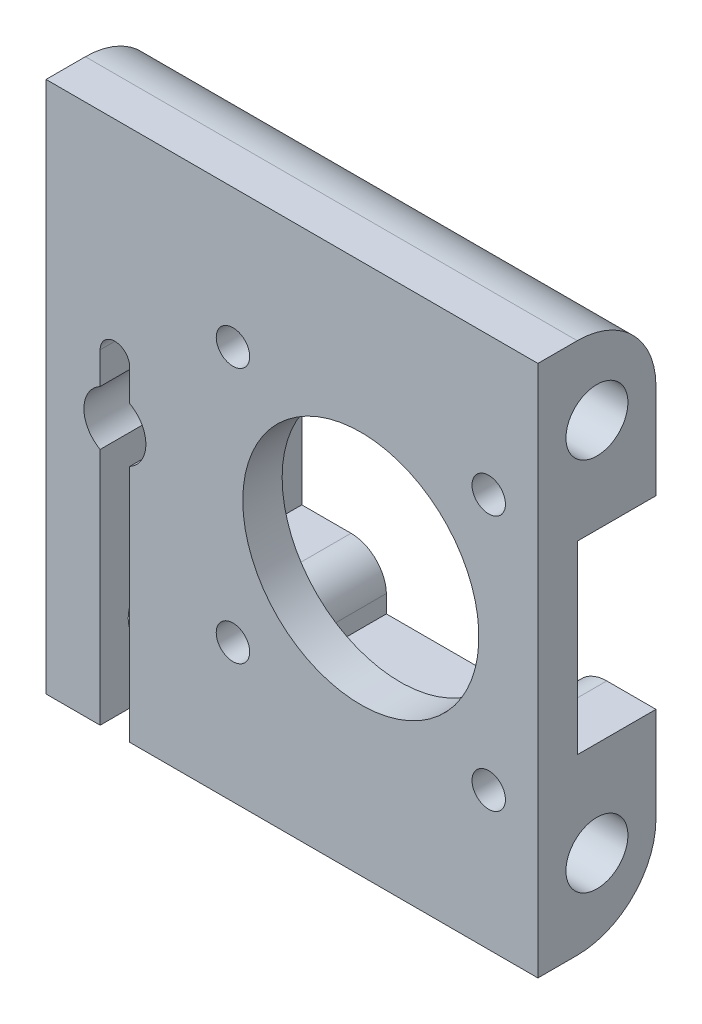
SolidWorks part; units mm, degrees
ref_plane "Front Plane" through (0, 0, 0) normal (0, 0, 1) x (1, 0, 0)
ref_plane "Top Plane" through (0, 0, 0) normal (0, 1, 0) x (1, 0, 0)
ref_plane "Right Plane" through (0, 0, 0) normal (1, 0, 0) x (0, 0, -1)
sketch "Sketch1" plane through (0, 0, 0) normal (0, 0, 1) x (1, 0, 0)
  line L1 (0, 0) -> (50, 0)
  line L2 (0, 0) -> (0, 54.105)
  line L3 (0, 54.105) -> (50, 54.105)
  line L4 (50, 0) -> (50, 54.105)
  dimension "D1" = 54.105
  dimension "D2" = 50
extrude "Boss-Extrude1" add sketch "Sketch1" along normal blind 12
sketch "Sketch2" plane through (0, 0, 0) normal (1, 0, 0) x (0, 0, -1)
  line L0 (-12, 27.0525) -> (0, 27.0525) construction
  line L1 (-12, 0) -> (-12, 54.105) construction
  line L2 (0, 0) -> (0, 54.105) construction
  circle A0 centre (-6, 46.105) radius 3.15
  circle A1 centre (-6, 8) radius 3.15
  dimension "D2" = 6.3
  dimension "D1" = 6
  dimension "D3" = 19.0525
extrude "Cut-Extrude1" cut sketch "Sketch2" along normal through all
fillet "Fillet1" radius 8 2 edges at (25, 0, 0) (25, 54.105, 0)
sketch "Sketch3" plane through (0, 0, 0) normal (0, 0, -1) x (-1, 0, 0)
  line L0 (-50, 27.0525) -> (0, 27.0525) construction
  line L1 (-50, 8) -> (-50, 46.105) construction
  line L2 (0, 46.105) -> (0, 8) construction
  line L3 (-8.5, 0) -> (-8.5, 24.2826)
  line L5 (-5.5, 33.0525) -> (-5.5, 29.8224)
  line L6 (0, 0) -> (-50, 0) construction
  line L7 (-8.5, 0) -> (-5.5, 0)
  line L8 (-8.5, 29.8224) -> (-8.5, 33.0525)
  line L9 (-5.5, 24.2826) -> (-5.5, 0)
  arc A0 (-8.5, 29.8224) -> (-8.5, 24.2826) centre (-7, 27.0525) ccw
  circle A1 centre (-32, 27.0525) radius 12
  circle A2 centre (-19, 40.0525) radius 1.7
  circle A3 centre (-19, 14.0525) radius 1.7
  arc A4 (-5.5, 24.2826) -> (-5.5, 29.8224) centre (-7, 27.0525) ccw
  arc A5 (-5.5, 33.0525) -> (-8.5, 33.0525) centre (-7, 33.0525) ccw
  circle A6 centre (-45, 14.0525) radius 1.7
  circle A7 centre (-45, 40.0525) radius 1.7
  dimension "D1" = 24
  dimension "D2" = 6.3
  dimension "D5" = 3.4
  dimension "D6" = 1.5
  dimension "D7" = 13
  dimension "D10" = 13
  dimension "D3" = 7
  dimension "D4" = 25
  dimension "D8" = 3
  dimension "D9" = 6
  dimension "D11" = 4
extrude "Cut-Extrude2" cut sketch "Sketch3" against normal through all
sketch "Sketch5" plane through (0, 0, 0) normal (0, 0, -1) x (-1, 0, 0)
  line L0 (-50, 27.0525) -> (-29.1332, 27.0525) construction
  line L1 (-19, 17.6525) -> (-14, 17.6525)
  line L2 (-50, 36.4525) -> (-50, 17.6525)
  line L4 (-14, 36.4525) -> (-14, 17.6525)
  line L5 (-50, 8) -> (-50, 46.105) construction
  line L7 (0, 46.105) -> (0, 8) construction
  line L8 (-41.4013, 41.7525) -> (-22.5987, 41.7525)
  line L9 (-22.5987, 41.7525) -> (-22.5987, 39.955)
  line L10 (-41.4013, 39.955) -> (-41.4013, 41.7525)
  line L11 (-45, 36.4525) -> (-50, 36.4525)
  line L12 (-19, 36.4525) -> (-14, 36.4525)
  line L13 (-45, 17.6525) -> (-50, 17.6525)
  line L14 (-41.4013, 14.15) -> (-41.4013, 12.3525)
  line L15 (-22.5987, 12.3525) -> (-22.5987, 14.15)
  line L16 (-41.4013, 12.3525) -> (-22.5987, 12.3525)
  arc A0 (-45, 36.4525) -> (-41.4013, 39.955) centre (-45, 40.0525) ccw
  arc A1 (-22.5987, 39.955) -> (-19, 36.4525) centre (-19, 40.0525) ccw
  circle A2 centre (-45, 40.0525) radius 1.7 construction
  circle A3 centre (-19, 40.0525) radius 1.7 construction
  arc A4 (-22.5987, 14.15) -> (-19, 17.6525) centre (-19, 14.0525) cw
  arc A5 (-45, 17.6525) -> (-41.4013, 14.15) centre (-45, 14.0525) cw
  dimension "D5" = 3.6
  dimension "D4" = 14
extrude "Cut-Extrude4" cut sketch "Sketch5" against normal offset from surface (8 mm away) 4 up to face at (43.3, 40.0525, 12)
sketch "Sketch4" plane through (0, 0, 0) normal (0, 0, -1) x (-1, 0, 0)
  circle A0 centre (-32, 27.0525) radius 6.7
  circle A1 centre (-32, 27.0525) radius 12 construction
  dimension "D1" = 13.4
extrude "Cut-Extrude3" [suppressed] cut sketch "Sketch4" against normal offset from surface (9 mm away) 3
